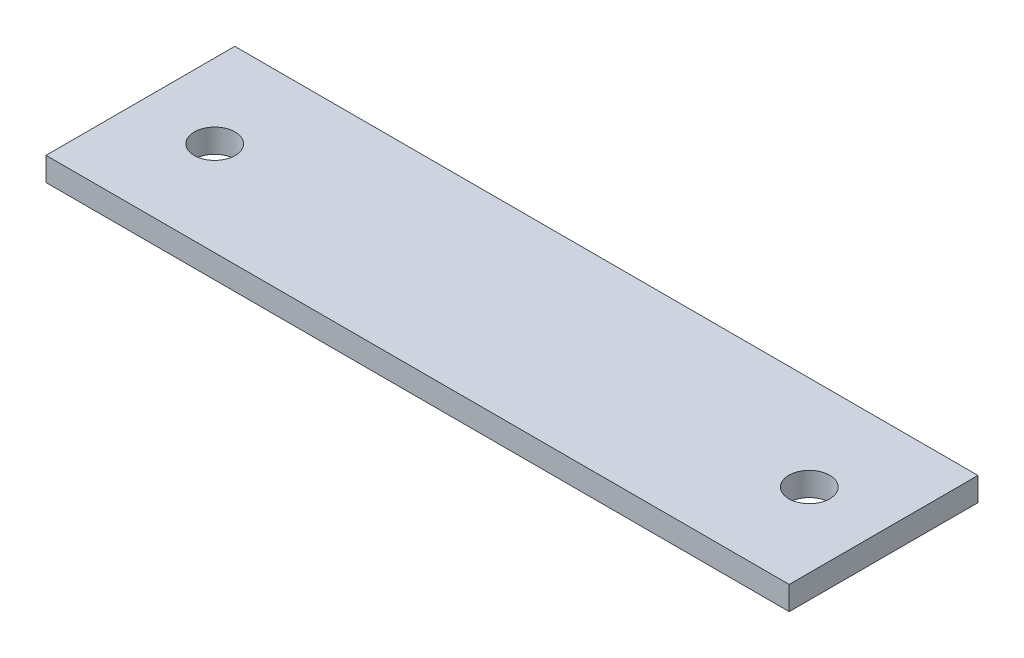
SolidWorks part; units mm, degrees
ref_plane "Front Plane" through (0, 0, 0) normal (0, 0, 1) x (1, 0, 0)
ref_plane "Top Plane" through (0, 0, 0) normal (0, 1, 0) x (1, 0, 0)
ref_plane "Right Plane" through (0, 0, 0) normal (1, 0, 0) x (0, 0, -1)
sketch "Sketch1" plane through (0, 0, 0) normal (0, 1, 0) x (1, 0, 0)
  line L1 (0, 0) -> (100, 0)
  line L2 (0, 0) -> (0, 25.4)
  line L3 (0, 25.4) -> (100, 25.4)
  line L4 (100, 0) -> (100, 25.4)
  dimension "D1" = 25.4
  dimension "D2" = 100
extrude "Boss-Extrude1" add sketch "Sketch1" along normal blind 3.175
sketch "Sketch2" plane through (0, 3.175, 0) normal (0, 1, 0) x (1, 0, 0)
  line L0 (0, 12.7) -> (100, 12.7) construction
  line L1 (0, 25.4) -> (0, 0) construction
  line L2 (100, 0) -> (100, 25.4) construction
  line L3 (50, 25.4) -> (50, 0) construction
  line L4 (100, 25.4) -> (0, 25.4) construction
  line L5 (0, 0) -> (100, 0) construction
  point P12 (90, 12.7)
  point P13 (0, 0)
  point P14 (10, 12.7)
  dimension "D1" = 10
hole_wizard "M5 Clearance Hole1" positions "3DSketch1" profile "Sketch3" hole size "M5" standard "ANSI Metric"
sketch3d "3DSketch1"
  point P0 (10, 3.175, -12.7)
  point P3 (90, 3.175, -12.7)
sketch "Sketch3" plane through (10, 3.175, -12.7) normal (1, 0, 0) x (0, 0, 1)
  line L0 (0, 0) -> (0, 14.0984)
  line L1 (0, 14.0984) -> (2.75, 12.446)
  line L2 (2.75, 12.446) -> (2.75, 0)
  line L5 (2.75, 0) -> (0, 0)
  line L10 (0, 14.0984) -> (-2.75, 12.446) construction
  line L11 (0, -6.35) -> (0, 107.95) construction
  dimension "Hole Dia." = 5.5
  dimension "Hole Depth" = 12.446
  dimension "Drill Angle" = 118
